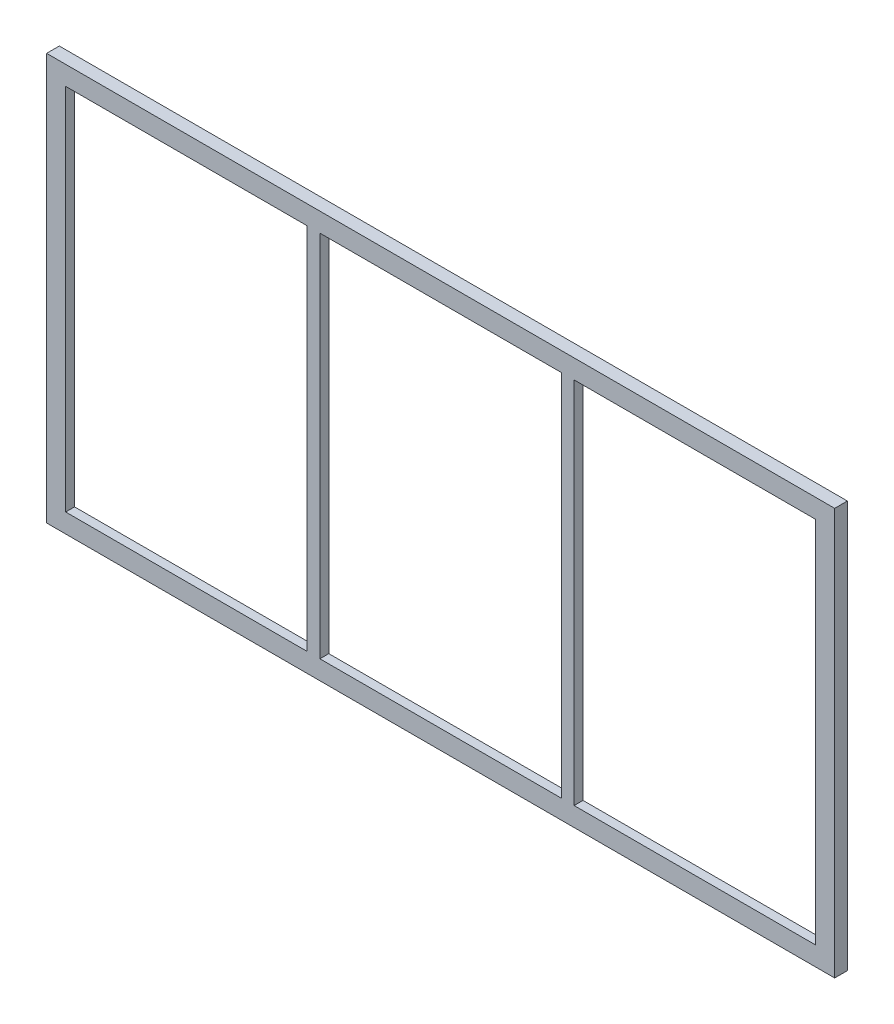
SolidWorks part; units mm, degrees
ref_plane "Alzado" through (0, 0, 0) normal (0, 0, 1) x (1, 0, 0)
ref_plane "Planta" through (0, 0, 0) normal (0, 1, 0) x (1, 0, 0)
ref_plane "Vista lateral" through (0, 0, 0) normal (1, 0, 0) x (0, 0, -1)
sketch "Croquis1" plane through (0, 0, 0) normal (0, 0, 1) x (1, 0, 0)
  line L0 (5, 295) -> (195, 295)
  line L1 (0, 0) -> (600, 0) construction
  line L2 (0, 0) -> (0, 300) construction
  line L3 (0, 300) -> (600, 300) construction
  line L4 (600, 0) -> (600, 300) construction
  line L5 (595, 5) -> (595, 295)
  line L6 (5, 5) -> (195, 5)
  line L7 (5, 5) -> (5, 295)
  line L8 (-10, 310) -> (610, 310)
  line L9 (610, -10) -> (610, 310)
  line L10 (-10, -10) -> (610, -10)
  line L11 (-10, -10) -> (-10, 310)
  line L12 (200, 300) -> (200, 0) construction
  line L13 (400, 300) -> (400, 0) construction
  line L14 (195, 295) -> (195, 5)
  line L15 (395, 295) -> (395, 5)
  line L16 (205, 295) -> (205, 5)
  line L17 (405, 295) -> (405, 5)
  line L18 (195, 300) -> (195, 0) construction
  line L19 (205, 295) -> (395, 295)
  line L20 (5, 295) -> (595, 295) construction
  line L21 (205, 300) -> (205, 0) construction
  line L22 (205, 5) -> (395, 5)
  line L23 (5, 5) -> (595, 5) construction
  line L24 (405, 300) -> (405, 0) construction
  line L25 (405, 5) -> (595, 5)
  line L26 (395, 300) -> (395, 0) construction
  line L27 (405, 295) -> (595, 295)
  dimension "D1" = 600
  dimension "D2" = 300
  dimension "D5" = 200
  dimension "D6" = 200
  dimension "D7" = 5
  dimension "D3" = 5
  dimension "D4" = 10
  dimension "D8" = 5
extrude "Saliente-Extruir1" add sketch "Croquis1" along normal blind 10
sketch "Croquis2" plane through (0, 0, 0) normal (0, 0, -1) x (-1, 0, 0)
  line L1 (0, 0) -> (-600, 0)
  line L2 (0, 0) -> (0, 300)
  line L3 (0, 300) -> (-600, 300)
  line L4 (-600, 0) -> (-600, 300)
  dimension "D1" = 600
  dimension "D2" = 300
extrude "Cortar-Extruir1" cut sketch "Croquis2" against normal blind 3
